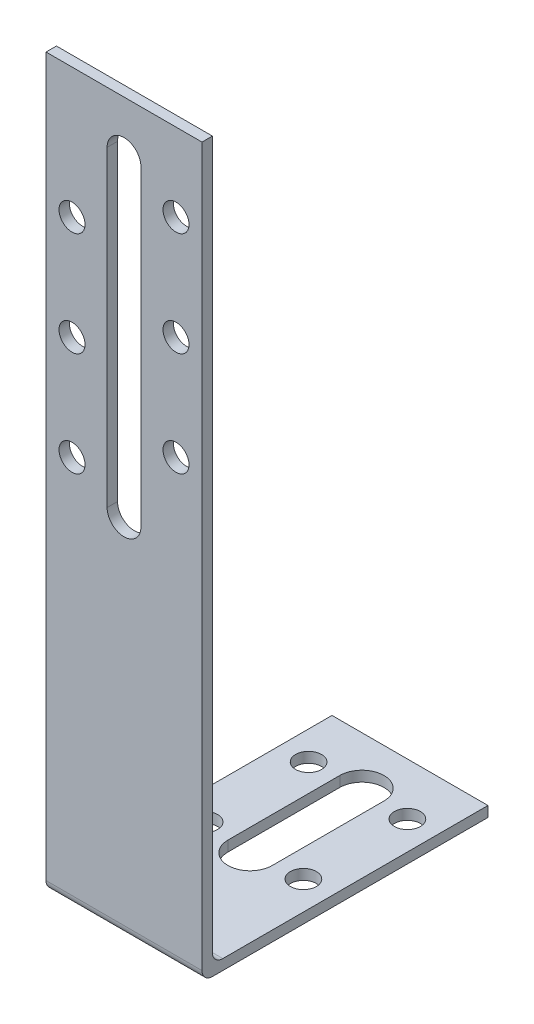
SolidWorks part; units mm, degrees
ref_plane "Plan de face" through (0, 0, 0) normal (0, 0, 1) x (1, 0, 0)
ref_plane "Plan de dessus" through (0, 0, 0) normal (0, 1, 0) x (1, 0, 0)
ref_plane "Plan de droite" through (0, 0, 0) normal (1, 0, 0) x (0, 0, -1)
sketch "Esquisse1" plane through (0, 0, 0) normal (1, 0, 0) x (0, 0, -1)
  line L0 (0, 0) -> (0, 140)
  line L1 (0, 140) -> (2, 140)
  line L2 (2, 140) -> (2, 2)
  line L3 (2, 2) -> (55, 2)
  line L4 (55, 2) -> (55, 0)
  line L5 (55, 0) -> (0, 0)
  dimension "D1" = 2
  dimension "D2" = 2
  dimension "D3" = 140
  dimension "D4" = 55
extrude "Boss.-Extru.1" add sketch "Esquisse1" along normal mid plane 30
fillet "Congé1" radius 2 2 edges at (0, 0, 0) (0, 2, -2)
sketch "Esquisse2" plane through (0, 2, 0) normal (0, 1, 0) x (1, 0, 0)
  line L0 (0, 24.25) -> (0, 45.75) construction
  line L1 (-4.25, 24.25) -> (-4.25, 45.75)
  line L2 (4.25, 24.25) -> (4.25, 45.75)
  line L4 (15, 55) -> (-15, 55) construction
  line L5 (15, 55) -> (15, 4) construction
  line L6 (-15, 35) -> (15, 35) construction
  line L8 (-15, 55) -> (-15, 4) construction
  line L9 (0, 55) -> (0, 2) construction
  line L10 (15, 2) -> (-15, 2) construction
  arc A0 (-4.25, 24.25) -> (4.25, 24.25) centre (0, 24.25) ccw
  arc A1 (4.25, 45.75) -> (-4.25, 45.75) centre (0, 45.75) ccw
  circle A2 centre (9.5, 45) radius 2.5
  circle A3 centre (9.5, 25) radius 2.5
  circle A4 centre (9.5, 45) radius 2.5
  circle A5 centre (9.5, 25) radius 2.5
  circle A6 centre (-9.5, 45) radius 2.5
  circle A7 centre (-9.5, 25) radius 2.5
  point P3 (0, 35)
  dimension "D1" = 4.25
  dimension "D6" = 5
  dimension "D2" = 21.5
  dimension "D3" = 9.25
  dimension "D4" = 10
  dimension "D5" = 5.5
extrude "Enlèv. mat.-Extru.1" cut sketch "Esquisse2" against normal up to next contours L2 A1 L1 A0 | A7 | A6 | A2 | A3
sketch "Esquisse4" plane through (0, 0, -2) normal (0, 0, -1) x (-1, 0, 0)
  line L0 (0, 130) -> (0, 70) construction
  line L1 (3.25, 130) -> (3.25, 70)
  line L2 (-3.25, 130) -> (-3.25, 70)
  line L3 (-15, 140) -> (15, 140) construction
  line L5 (15, 4) -> (15, 140) construction
  arc A0 (3.25, 130) -> (-3.25, 130) centre (0, 130) ccw
  arc A1 (-3.25, 70) -> (3.25, 70) centre (0, 70) ccw
  circle A2 centre (-10, 125) radius 2.5
  circle A3 centre (-10, 105) radius 2.5
  circle A4 centre (-10, 85) radius 2.5
  circle A5 centre (10, 115) radius 2.5
  circle A6 centre (10, 95) radius 2.5
  circle A7 centre (10, 75) radius 2.5
  point P3 (0, 100)
  dimension "D1" = 3.25
  dimension "D5" = 5
  dimension "D9" = 5
  dimension "D11" = 25
  dimension "D13" = 20
  dimension "D2" = 60
  dimension "D3" = 10
  dimension "D4" = 10
  dimension "D6" = 15
  dimension "D8" = 20
  dimension "D10" = 5
  dimension "D7" = 3
  dimension "D12" = 3
extrude "Enlèv. mat.-Extru.2" cut sketch "Esquisse4" against normal up to next
